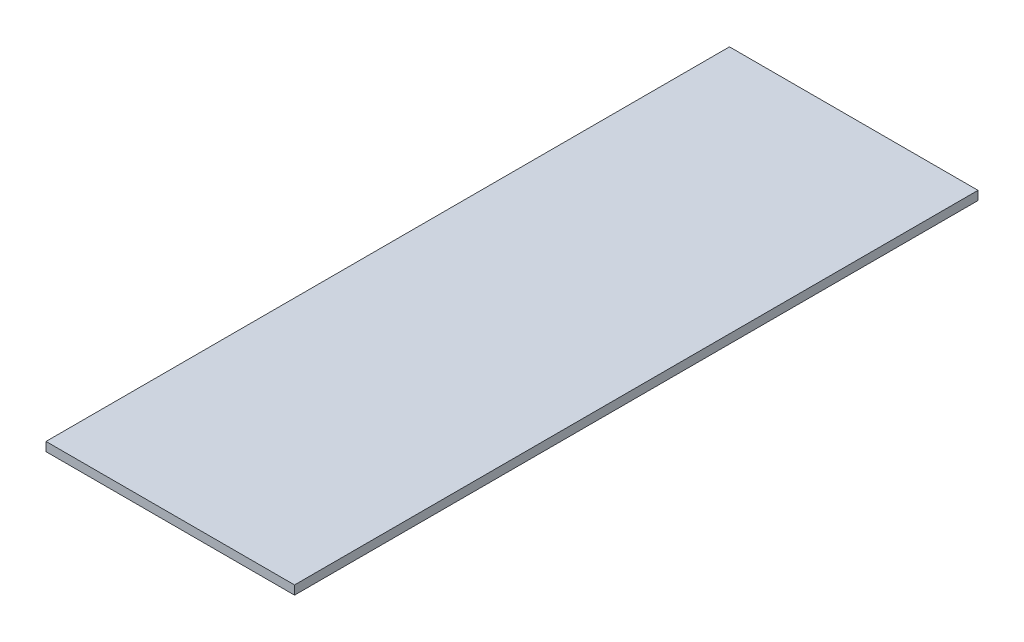
SolidWorks part; units mm, degrees
ref_plane "Front Plane" through (0, 0, 0) normal (0, 0, 1) x (1, 0, 0)
ref_plane "Top Plane" through (0, 0, 0) normal (0, 1, 0) x (1, 0, 0)
ref_plane "Right Plane" through (0, 0, 0) normal (1, 0, 0) x (0, 0, -1)
sketch "Sketch1" plane through (0, 0, 0) normal (0, 1, 0) x (1, 0, 0)
  line L0 (-28, -77) -> (-28, 77)
  line L1 (-23, -72) -> (23, -72) construction
  line L2 (-23, -72) -> (-23, 72) construction
  line L3 (-23, 72) -> (23, 72) construction
  line L4 (23, -72) -> (23, 72) construction
  line L5 (-23, -72) -> (23, 72) construction
  line L6 (-23, 72) -> (23, -72) construction
  line L7 (-28, 77) -> (28, 77)
  line L8 (28, -77) -> (28, 77)
  line L9 (-28, -77) -> (28, -77)
  point P0 (0, 0)
  dimension "D1" = 144
  dimension "D2" = 46
  dimension "D3" = 5
extrude "Boss-Extrude1" add sketch "Sketch1" along normal blind 2
